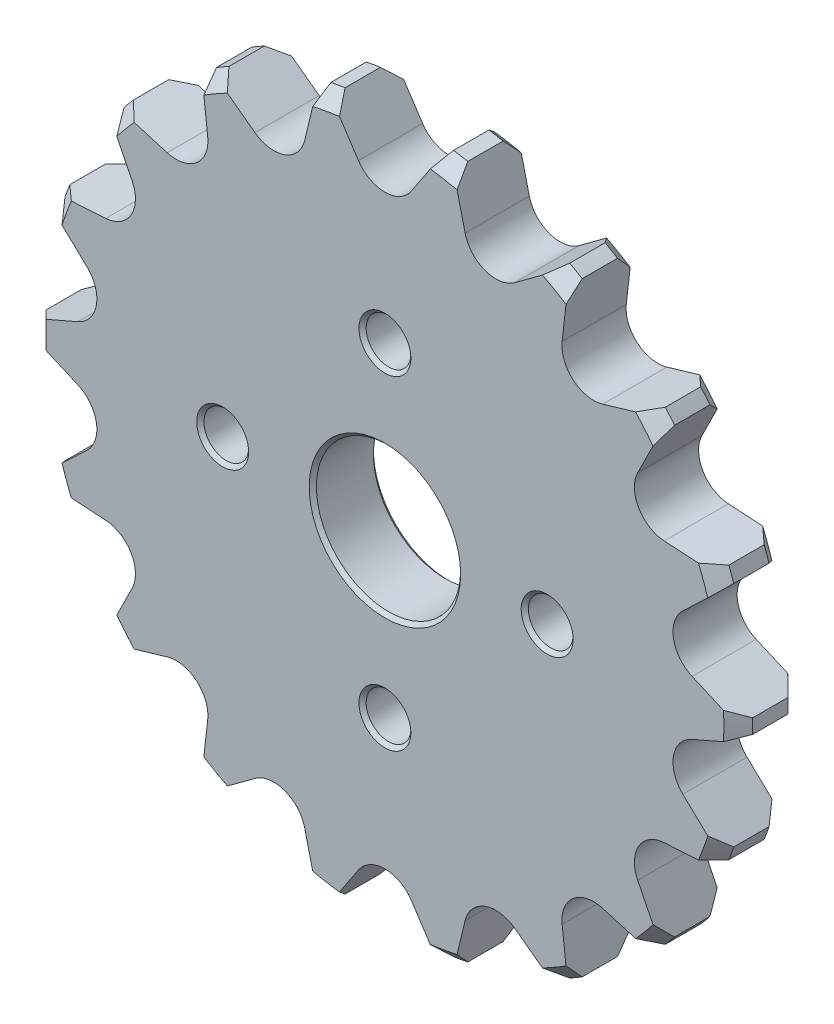
SolidWorks part; units mm, degrees
material "1.0037 (S235JR)"
ref_plane "Płaszczyzna przednia" through (0, 0, 0) normal (0, 0, 1) x (1, 0, 0)
ref_plane "Płaszczyzna górna" through (0, 0, 0) normal (0, 1, 0) x (1, 0, 0)
ref_plane "Płaszczyzna prawa" through (0, 0, 0) normal (1, 0, 0) x (0, 0, -1)
sketch "Szkic1" plane through (0, 0, 0) normal (0, 0, 1) x (1, 0, 0)
  circle A0 centre (0, 0) radius 49
  dimension "D1" = 98
extrude "Dodanie-wyciągnięcie1" add sketch "Szkic1" along normal blind 8.9
chamfer "Sfazowanie1" distance 2 angle 45 2 edges at (49, 0, 8.9) (49, 0, 0)
sketch "Szkic2" plane through (0, 0, 0) normal (0, 0, 1) x (-1, 0, 0)
  line L0 (0, 0) -> (0, 49) construction
  line L5 (7.5222, 48.4192) -> (5.3333, 45.1141)
  line L6 (5.3333, 45.1141) -> (3.6684, 42.6004)
  line L7 (-3.6684, 42.6004) -> (-5.3333, 45.1141)
  line L8 (-5.3333, 45.1141) -> (-7.5222, 48.4192)
  arc A2 (7.5222, 48.4192) -> (-7.5222, 48.4192) centre (0, 0) ccw
  arc A4 (-3.6684, 42.6004) -> (3.6684, 42.6004) centre (0, 45.03) ccw
extrude "Wytnij-wyciągnięcie1" cut sketch "Szkic2" along normal blind 8.9
pattern_circular "Szyk kołowy1" count 18 over 360 about axis through (0, 0, 0) along (0, 0, 1) of "Wytnij-wyciągnięcie1"
sketch "Szkic3" plane through (0, 0, 8.9) normal (0, 0, 1) x (1, 0, 0)
  circle A0 centre (0, 0) radius 10
  dimension "D1" = 20
extrude "Wytnij-wyciągnięcie2" cut sketch "Szkic3" against normal up to next
sketch "Szkic4" plane through (0, 0, 8.9) normal (0, 0, 1) x (1, 0, 0)
  circle A0 centre (0, 0) radius 22.5 construction
  circle A1 centre (0, 22.5) radius 3.1
  circle A2 centre (0, 0) radius 22.5 construction
  circle A3 centre (22.5, 0) radius 3.1
  circle A4 centre (0, 0) radius 22.5 construction
  circle A5 centre (0, -22.5) radius 3.1
  circle A6 centre (0, 0) radius 22.5 construction
  circle A7 centre (-22.5, 0) radius 3.1
  point P17 (0, 0)
  dimension "D1" = 45
  dimension "D2" = 6.2
  dimension "D3" = 4
extrude "Wytnij-wyciągnięcie3" cut sketch "Szkic4" against normal up to next
chamfer "Sfazowanie2" distance 0.5 angle 45 10 edges at (3.1, 22.5, 0) (3.1, 22.5, 8.9) (-19.4, 0, 0) (-19.4, 0, 8.9) (3.1, -22.5, 0) (3.1, -22.5, 8.9) (25.6, 0, 0) (25.6, 0, 8.9) (10, 0, 0) (10, 0, 8.9)
